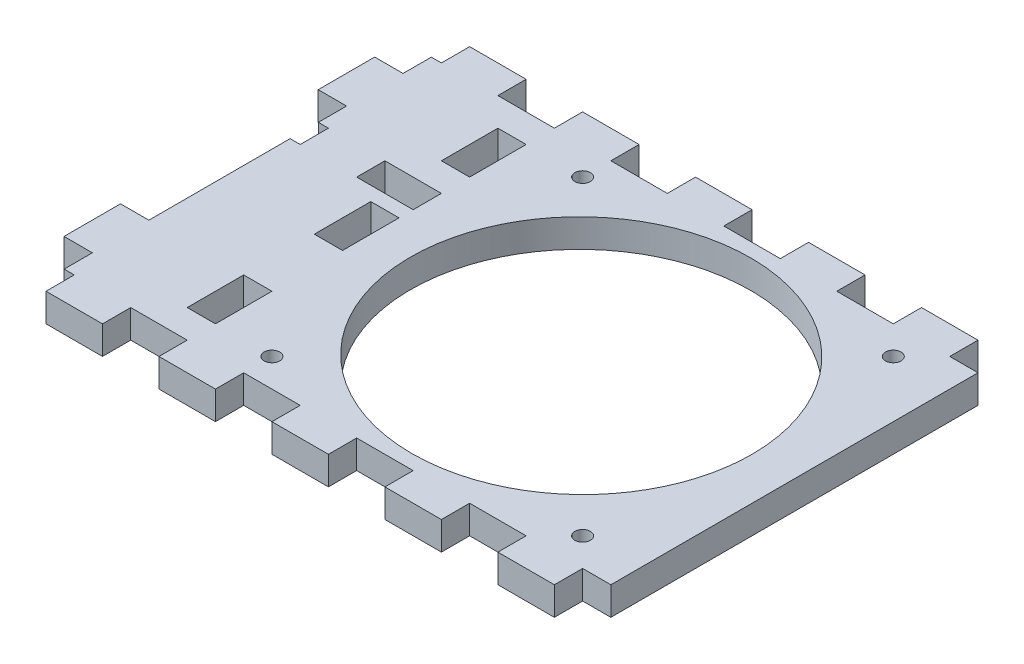
SolidWorks part; units mm, degrees
ref_plane "Front Plane" through (0, 0, 0) normal (0, 0, 1) x (1, 0, 0)
ref_plane "Top Plane" through (0, 0, 0) normal (0, 1, 0) x (1, 0, 0)
ref_plane "Right Plane" through (0, 0, 0) normal (1, 0, 0) x (0, 0, -1)
sketch "Sketch4" plane through (0, 0, 0) normal (0, 0, 1) x (1, 0, 0)
  line L0 (0, 0) -> (40.3547, 419.1) construction
  line L1 (40.3547, 419.1) -> (159.2585, 419.1) construction
  line L2 (159.2585, 419.1) -> (159.2585, 0) construction
  line L3 (159.2585, 0) -> (0, 0) construction
  line L4 (159.2585, -1000) -> (159.2585, 49000) construction
  line L5 (2.0164, 20.9415) -> (40.3547, 419.1) construction
  line L6 (2.0164, 20.9415) -> (41.8323, 17.1077) construction
  line L7 (40.3547, 419.1) -> (80.1706, 415.2662) construction
  line L8 (41.8323, 17.1077) -> (80.1706, 415.2662) construction
  line L9 (64.0085, -1000) -> (64.0085, 49000) construction
  line L10 (-42.7214, 317.5) -> (-118.5706, 324.8034) construction
  line L11 (-20.0013, 414.3375) -> (40.196, 414.3375) construction
  line L12 (-1162.1335, 304.8) -> (48837.8665, 304.8) construction
  line L13 (-120.1415, 292.1) -> (-43.9415, 292.1) construction
  line L14 (-118.5706, 324.8034) -> (-43.9415, 292.1) construction
  line L15 (-42.7214, 317.5) -> (-120.1415, 292.1) construction
  line L16 (40.196, 338.1375) -> (-20.0013, 338.1375) construction
  line L17 (-128.0517, 325.7164) -> (29.8985, 310.5075)
  line L18 (-128.0517, 325.7164) -> (-127.4431, 332.0371)
  line L19 (-127.4431, 332.0371) -> (40.3547, 419.1)
  line L20 (40.3547, 419.1) -> (108.4585, 419.1)
  line L21 (108.4585, 419.1) -> (108.4585, 0) construction
  line L22 (29.8985, 310.5075) -> (0.4102, 4.2603)
  line L23 (0.4102, 4.2603) -> (44.6556, 0)
  line L24 (44.6556, 0) -> (108.4585, 0)
  line L25 (108.4585, 419.1) -> (159.2585, 311.15)
  line L26 (159.2585, 311.15) -> (159.2585, 304.8)
  line L27 (159.2585, 304.8) -> (108.4585, 280.8941)
  line L28 (108.4585, 280.8941) -> (108.4585, 0)
  line L29 (30.0189, 311.7586) -> (36.3397, 311.15) construction
  arc A0 (-118.5706, 324.8034) -> (-20.0013, 414.3375) centre (-20.0013, 315.3123) cw construction
  arc A1 (73.5335, 304.8) -> (40.196, 338.1375) centre (40.196, 304.8) ccw construction
  arc A2 (149.7335, 304.8) -> (40.196, 414.3375) centre (40.196, 304.8) ccw construction
  arc A3 (-42.7214, 317.5) -> (-20.0013, 338.1375) centre (-20.0013, 315.3123) cw construction
  point P7 (57.6585, 400.05)
  point P17 (149.7335, 304.8)
  point P18 (73.5335, 304.8)
  dimension "D9" = 9.525
  dimension "D14" = 25.4
  dimension "D1" = 419.1
  dimension "D2" = 101.6
  dimension "D3" = 19.05
  dimension "D4" = 19.05
  dimension "D5" = 84.5
  dimension "D6" = 40
  dimension "D7" = 400
  dimension "D8" = 95.25
  dimension "D10" = 9.525
  dimension "D11" = 114.3
  dimension "D12" = 76.2
  dimension "D13" = 9.525
  dimension "D15" = 127
  dimension "D16" = 9.525
  dimension "D17" = 203.2
  dimension "D18" = 6.35
  dimension "D19" = 50.8
  dimension "D20" = 44.45
  dimension "D21" = 6.35
  dimension "D22" = 6.35
  dimension "D23" = 6.35
sketch "Sketch5" plane through (0, 0, 0) normal (0, 0, 1) x (1, 0, 0)
  line L0 (0, 0) -> (40.3547, 419.1) construction
  line L1 (159.2585, 304.8) -> (29.9603, 304.8)
  line L2 (159.2585, 304.8) -> (159.2585, 311.15)
  line L3 (159.2585, 311.15) -> (29.9603, 311.15)
  line L4 (29.9603, 304.8) -> (29.9603, 311.15)
extrude "Boss-Extrude1" add sketch "Sketch5" along normal blind 95.25
sketch "Sketch6" plane through (0, 311.15, 0) normal (0, 1, 0) x (1, 0, 0)
  line L0 (159.2585, -47.625) -> (111.6335, -47.625) construction
  line L1 (159.2585, -95.25) -> (159.2585, 0) construction
  line L2 (72.9232, 0) -> (72.9232, -47.625) construction
  line L3 (146.5585, -82.55) -> (76.7085, -82.55) construction
  line L4 (146.5585, -82.55) -> (146.5585, -12.7) construction
  line L5 (146.5585, -12.7) -> (76.7085, -12.7) construction
  line L6 (76.7085, -82.55) -> (76.7085, -12.7) construction
  line L7 (146.5585, -82.55) -> (76.7085, -12.7) construction
  line L8 (146.5585, -12.7) -> (76.7085, -82.55) construction
  line L9 (159.2585, 0) -> (29.9603, 0) construction
  line L12 (149.7335, 0) -> (149.7335, -47.625) construction
  circle A1 centre (76.7085, -12.7) radius 1.75
  circle A2 centre (76.7085, -82.55) radius 1.75
  circle A3 centre (146.5585, -82.55) radius 1.75
  circle A4 centre (146.5585, -12.7) radius 1.75
  ellipse E0 centre (111.3284, -47.625) end of major axis (149.7335, -47.625) minor radius 38.1
  dimension "D1" = 76.2
  dimension "D4" = 3.5
  dimension "D2" = 47.625
  dimension "D3" = 69.85
extrude "Cut-Extrude3" cut sketch "Sketch6" against normal through all
sketch "Sketch7" plane through (0, 311.15, 0) normal (0, 1, 0) x (1, 0, 0)
  line L0 (159.2585, 0) -> (29.9603, 0) construction
  line L1 (152.9085, 0) -> (165.6085, 0)
  line L2 (152.9085, 0) -> (152.9085, -6.35)
  line L3 (152.9085, -6.35) -> (165.6085, -6.35)
  line L4 (165.6085, 0) -> (165.6085, -6.35)
  line L5 (159.2585, -95.25) -> (29.9603, -95.25) construction
  line L6 (152.9085, -95.25) -> (165.6085, -95.25)
  line L7 (152.9085, -95.25) -> (152.9085, -88.9)
  line L8 (152.9085, -88.9) -> (165.6085, -88.9)
  line L9 (165.6085, -95.25) -> (165.6085, -88.9)
  line L10 (159.2585, -95.25) -> (159.2585, 0) construction
  dimension "D1" = 6.35
  dimension "D2" = 12.7
  dimension "D3" = 6.35
extrude "Cut-Extrude4" cut sketch "Sketch7" against normal through all
pattern_linear "LPattern1" count 17 spacing 25.4 along (-1, 0, 0) of "Cut-Extrude4"
sketch "Sketch8" plane through (0, 311.15, 0) normal (0, 1, 0) x (1, 0, 0)
  line L0 (159.2585, -88.9) -> (159.2585, -6.35) construction
  line L1 (25.9085, -38.1) -> (38.6085, -38.1)
  line L2 (25.9085, -38.1) -> (25.9085, -31.75)
  line L3 (25.9085, -31.75) -> (38.6085, -31.75)
  line L4 (38.6085, -38.1) -> (38.6085, -31.75)
  line L5 (51.3085, -38.1) -> (64.0085, -38.1)
  line L6 (51.3085, -38.1) -> (51.3085, -31.75)
  line L7 (51.3085, -31.75) -> (64.0085, -31.75)
  line L8 (64.0085, -38.1) -> (64.0085, -31.75)
  line L9 (51.3085, 0) -> (38.6085, 0) construction
  dimension "D1" = 6.35
  dimension "D2" = 95.25
  dimension "D3" = 12.7
  dimension "D4" = 12.7
  dimension "D5" = 31.75
extrude "Cut-Extrude5" cut sketch "Sketch8" against normal through all
sketch "Sketch9" plane through (0, 311.15, 0) normal (0, 1, 0) x (1, 0, 0)
  line L0 (159.2585, -47.625) -> (57.6585, -47.625) construction
  line L1 (57.6585, -53.975) -> (64.0085, -53.975)
  line L2 (57.6585, -53.975) -> (57.6585, -41.275)
  line L3 (57.6585, -41.275) -> (64.0085, -41.275)
  line L4 (64.0085, -53.975) -> (64.0085, -41.275)
  line L5 (64.0085, -25.4) -> (57.6585, -25.4)
  line L6 (64.0085, -25.4) -> (64.0085, -12.7)
  line L7 (64.0085, -12.7) -> (57.6585, -12.7)
  line L8 (57.6585, -25.4) -> (57.6585, -12.7)
  line L9 (159.2585, -88.9) -> (159.2585, -6.35) construction
  line L10 (64.0085, -38.1) -> (64.0085, -31.75) construction
  line L11 (76.7085, 0) -> (64.0085, 0) construction
  line L12 (57.6585, -69.85) -> (64.0085, -69.85)
  line L13 (57.6585, -69.85) -> (57.6585, -82.55)
  line L14 (57.6585, -82.55) -> (64.0085, -82.55)
  line L15 (64.0085, -69.85) -> (64.0085, -82.55)
  line L16 (76.7085, -95.25) -> (64.0085, -95.25) construction
  dimension "D1" = 12.7
  dimension "D2" = 6.35
  dimension "D3" = 12.7
  dimension "D4" = 12.7
extrude "Cut-Extrude6" cut sketch "Sketch9" against normal through all
sketch "Sketch10" plane through (0, 311.15, 0) normal (0, 1, 0) x (1, 0, 0)
  line L0 (29.9603, -31.75) -> (29.9603, -6.35) construction
  line L1 (29.9603, -6.35) -> (36.3397, -6.35)
  line L2 (29.9603, -6.35) -> (29.9603, -12.7)
  line L3 (29.9603, -12.7) -> (36.3397, -12.7)
  line L4 (36.3397, -6.35) -> (36.3397, -12.7)
  line L5 (29.9603, -25.4) -> (36.3397, -25.4)
  line L6 (29.9603, -25.4) -> (29.9603, -69.85)
  line L7 (29.9603, -69.85) -> (36.3397, -69.85)
  line L8 (36.3397, -25.4) -> (36.3397, -69.85)
  line L9 (51.3085, 0) -> (38.6085, 0) construction
  line L10 (29.9603, -88.9) -> (36.3397, -88.9)
  line L11 (29.9603, -88.9) -> (29.9603, -82.55)
  line L12 (29.9603, -82.55) -> (36.3397, -82.55)
  line L13 (36.3397, -88.9) -> (36.3397, -82.55)
  dimension "D1" = 12.7
  dimension "D2" = 12.7
  dimension "D3" = 12.7
extrude "Cut-Extrude7" cut sketch "Sketch10" against normal through all
